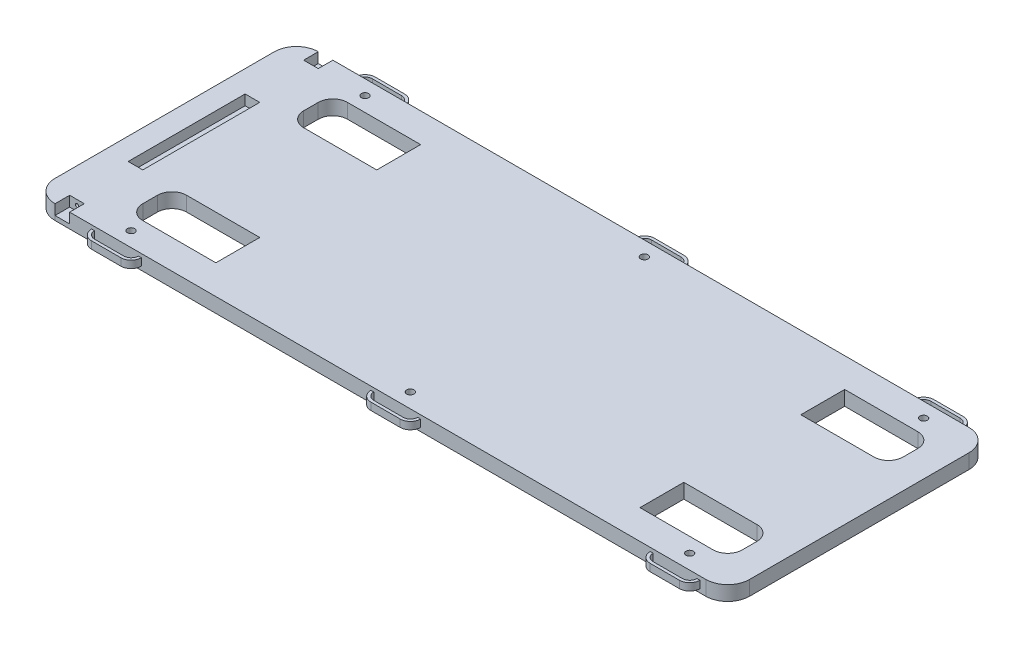
SolidWorks part; units mm, degrees
ref_plane "Front Plane" through (0, 0, 0) normal (0, 0, 1) x (1, 0, 0)
ref_plane "Top Plane" through (0, 0, 0) normal (0, 1, 0) x (1, 0, 0)
ref_plane "Right Plane" through (0, 0, 0) normal (1, 0, 0) x (0, 0, -1)
sketch "Main Body" plane through (0, 0, 0) normal (0, 1, 0) x (1, 0, 0)
  line L0 (-301.625, -95.25) -> (-301.625, 95.25)
  line L1 (-282.575, 114.3) -> (282.575, 114.3)
  line L2 (-282.575, -114.3) -> (282.575, -114.3)
  line L3 (301.625, 95.25) -> (301.625, -95.25)
  line L4 (-301.625, 0) -> (301.625, 0) construction
  arc A0 (-301.625, 95.25) -> (-282.575, 114.3) centre (-282.575, 95.25) cw
  arc A1 (-282.575, -114.3) -> (-301.625, -95.25) centre (-282.575, -95.25) cw
  arc A2 (282.575, 114.3) -> (301.625, 95.25) centre (282.575, 95.25) cw
  arc A3 (301.625, -95.25) -> (282.575, -114.3) centre (282.575, -95.25) cw
  point P14 (0, 0)
  dimension "D3" = 19.05
  dimension "D1" = 228.6
  dimension "D2" = 603.25
extrude "Boss-Extrude1" add sketch "Main Body" along normal blind 12.7
sketch "Sketch2" plane through (0, 0, 114.3) normal (0, 0, 1) x (1, 0, 0)
  line L0 (-282.575, 0) -> (282.575, 0) construction
  line L1 (-282.575, 12.7) -> (-260.35, 12.7)
  line L3 (-273.05, 0) -> (-260.35, 0)
sketch "Backrest Bracket Slot" plane through (0, 0, 114.3) normal (0, 0, 1) x (1, 0, 0)
  line L1 (-282.575, 12.7) -> (-269.875, 12.7)
  line L2 (-282.575, 12.7) -> (-282.575, 3.81)
  line L3 (-282.575, 3.81) -> (-269.875, 3.81)
  line L4 (-269.875, 12.7) -> (-269.875, 3.81)
  dimension "D1" = 12.7
  dimension "D2" = 8.89
extrude "Cut-Extrude3" cut sketch "Backrest Bracket Slot" against normal blind 12.7
sketch "Backrest Screw Hole" plane through (0, 0, 101.6) normal (0, 0, 1) x (1, 0, 0)
  line L0 (-282.575, 8.255) -> (-269.875, 8.255) construction
  line L1 (-282.575, 12.7) -> (-282.575, 3.81) construction
  line L2 (-269.875, 3.81) -> (-269.875, 12.7) construction
  circle A0 centre (-276.225, 8.255) radius 1.397
  dimension "D1" = 2.794
extrude "Cut-Extrude4" cut sketch "Backrest Screw Hole" against normal blind 6.35
mirror "Mirror1" about plane through (0, 0, 0) normal (0, 0, 1) of "Cut-Extrude4", "Cut-Extrude3"
sketch "Couch Foot Slits" plane through (0, 12.7, 0) normal (0, 1, 0) x (1, 0, 0)
  line L0 (-269.875, 101.6) -> (-269.875, -101.6) construction
  line L1 (-231.775, 88.9) -> (-168.275, 88.9)
  line L2 (-231.775, 50.8) -> (-168.275, 50.8)
  line L3 (-244.475, 76.2) -> (-244.475, 63.5)
  line L4 (276.225, 76.2) -> (276.225, 63.5)
  line L5 (-231.775, -50.8) -> (-168.275, -50.8)
  line L6 (-231.775, -88.9) -> (-168.275, -88.9)
  line L7 (-244.475, -63.5) -> (-244.475, -76.2)
  line L8 (276.225, -63.5) -> (276.225, -76.2)
  line L9 (301.625, -95.25) -> (301.625, 95.25) construction
  line L10 (282.575, 114.3) -> (-269.875, 114.3) construction
  line L12 (-269.875, -114.3) -> (282.575, -114.3) construction
  line L14 (200.025, 88.9) -> (263.525, 88.9)
  line L16 (-168.275, 88.9) -> (-168.275, 50.8)
  line L18 (200.025, 88.9) -> (200.025, 50.8)
  line L20 (-168.275, -50.8) -> (-168.275, -88.9)
  line L22 (200.025, -50.8) -> (200.025, -88.9)
  line L23 (200.025, 50.8) -> (263.525, 50.8)
  line L24 (200.025, -50.8) -> (263.525, -50.8)
  line L25 (200.025, -88.9) -> (263.525, -88.9)
  arc A0 (-244.475, 76.2) -> (-231.775, 88.9) centre (-231.775, 76.2) cw
  arc A1 (-231.775, 50.8) -> (-244.475, 63.5) centre (-231.775, 63.5) cw
  arc A2 (263.525, 88.9) -> (276.225, 76.2) centre (263.525, 76.2) cw
  arc A3 (276.225, 63.5) -> (263.525, 50.8) centre (263.525, 63.5) cw
  arc A4 (-244.475, -63.5) -> (-231.775, -50.8) centre (-231.775, -63.5) cw
  arc A5 (-231.775, -88.9) -> (-244.475, -76.2) centre (-231.775, -76.2) cw
  arc A6 (263.525, -50.8) -> (276.225, -63.5) centre (263.525, -63.5) cw
  arc A7 (276.225, -76.2) -> (263.525, -88.9) centre (263.525, -76.2) cw
  dimension "D6" = 12.7
  dimension "D9" = 12.7
  dimension "D1" = 25.4
  dimension "D2" = 25.4
  dimension "D3" = 25.4
  dimension "D4" = 25.4
  dimension "D5" = 101.6
  dimension "D7" = 76.2
  dimension "D8" = 76.2
extrude "Cut-Extrude5" cut sketch "Couch Foot Slits" against normal blind 25.4
ref_plane "Central Plane" through (0, 6.35, 0) normal (0, 1, 0) x (1, 0, 0)
sketch "Sketch24" plane through (0, 6.35, 0) normal (0, 1, 0) x (1, 0, 0)
  line L0 (-269.875, -114.3) -> (282.575, -114.3) construction
  line L1 (0.635, -120.65) -> (26.035, -120.65)
  line L2 (-248.285, -114.3) -> (-248.285, -101.5898) construction
  line L3 (-241.935, -120.65) -> (-216.535, -120.65)
  line L5 (-241.935, -123.19) -> (-216.535, -123.19)
  line L7 (-250.825, -114.3) -> (-248.285, -114.3)
  line L8 (-210.185, -114.3) -> (-207.645, -114.3)
  line L9 (32.385, -114.3) -> (34.925, -114.3)
  line L10 (0.635, -123.19) -> (26.035, -123.19)
  line L11 (-8.255, -114.3) -> (-5.715, -114.3)
  line L12 (243.205, -120.65) -> (268.605, -120.65)
  line L13 (274.955, -114.3) -> (277.495, -114.3)
  line L14 (243.205, -123.19) -> (268.605, -123.19)
  line L15 (234.315, -114.3) -> (236.855, -114.3)
  line L16 (-241.935, -120.65) -> (0.635, -120.65) construction
  arc A0 (-241.935, -120.65) -> (-248.285, -114.3) centre (-241.935, -114.3) cw
  arc A1 (-241.935, -123.19) -> (-250.825, -114.3) centre (-241.935, -114.3) cw
  arc A2 (-216.535, -123.19) -> (-207.645, -114.3) centre (-216.535, -114.3) ccw
  arc A3 (-216.535, -120.65) -> (-210.185, -114.3) centre (-216.535, -114.3) ccw
  arc A4 (26.035, -120.65) -> (32.385, -114.3) centre (26.035, -114.3) ccw
  arc A5 (26.035, -123.19) -> (34.925, -114.3) centre (26.035, -114.3) ccw
  arc A6 (0.635, -123.19) -> (-8.255, -114.3) centre (0.635, -114.3) cw
  arc A7 (0.635, -120.65) -> (-5.715, -114.3) centre (0.635, -114.3) cw
  arc A8 (268.605, -120.65) -> (274.955, -114.3) centre (268.605, -114.3) ccw
  arc A9 (268.605, -123.19) -> (277.495, -114.3) centre (268.605, -114.3) ccw
  arc A10 (243.205, -123.19) -> (234.315, -114.3) centre (243.205, -114.3) cw
  arc A11 (243.205, -120.65) -> (236.855, -114.3) centre (243.205, -114.3) cw
  dimension "D2" = 2.54
  dimension "D1" = 2.54
  dimension "D3" = 38.1
  dimension "D4" = 25.4
  dimension "D5" = 19.05
  dimension "D7" = 242.57
  dimension "D6" = 3
extrude "Boss-Extrude2" add sketch "Sketch24" along normal mid plane 6.35
mirror "Mirror2" about plane through (0, 0, 0) normal (0, 0, 1) of "Boss-Extrude2"
sketch "Sketch37" plane through (0, 12.7, 0) normal (0, 1, 0) x (1, 0, 0)
  line L0 (-282.575, 101.6) -> (-282.575, 114.3) construction
  line L1 (-282.575, 50.8) -> (-269.875, 50.8)
  line L2 (-282.575, 50.8) -> (-282.575, -50.8)
  line L3 (-282.575, -50.8) -> (-269.875, -50.8)
  line L4 (-269.875, 50.8) -> (-269.875, -50.8)
  line L5 (-269.875, 101.6) -> (-269.875, 114.3) construction
  line L6 (-276.225, 101.6) -> (-274.828, -101.6) construction
  line L7 (-269.875, 101.6) -> (-282.575, 101.6) construction
  point P13 (-269.875, 0)
  point P14 (-275.5265, 0)
  dimension "D1" = 101.6
extrude "Cut-Extrude7" cut sketch "Sketch37" against normal blind 8.89
sketch "Sketch38" plane through (0, 12.7, 0) normal (0, 1, 0) x (1, 0, 0)
  line L0 (-250.825, -114.3) -> (-207.645, -114.3) construction
  line L1 (-221.2987, -88.9) -> (-221.2987, -114.3) construction
  line L2 (-231.775, -88.9) -> (-168.275, -88.9) construction
  line L3 (-5.715, -114.3) -> (32.385, -114.3) construction
  line L4 (236.855, -114.3) -> (274.955, -114.3) construction
  circle A0 centre (-229.235, -101.6) radius 3.175
  circle A1 centre (13.335, -101.6) radius 3.175
  circle A2 centre (255.905, -101.6) radius 3.175
  point P6 (-229.235, -114.3)
  point P11 (-221.2987, -101.6)
  point P18 (13.335, -114.3)
  point P25 (255.905, -114.3)
  point P26 (255.905, -101.6)
  point P27 (0, 0)
  dimension "D1" = 6.35
extrude "Cut-Extrude8" cut sketch "Sketch38" against normal up to next (12.7 mm away)
mirror "Mirror3" about plane through (0, 0, 0) normal (0, 0, 1) of "Cut-Extrude8"
equation "\"0.4n\"=0.5"
